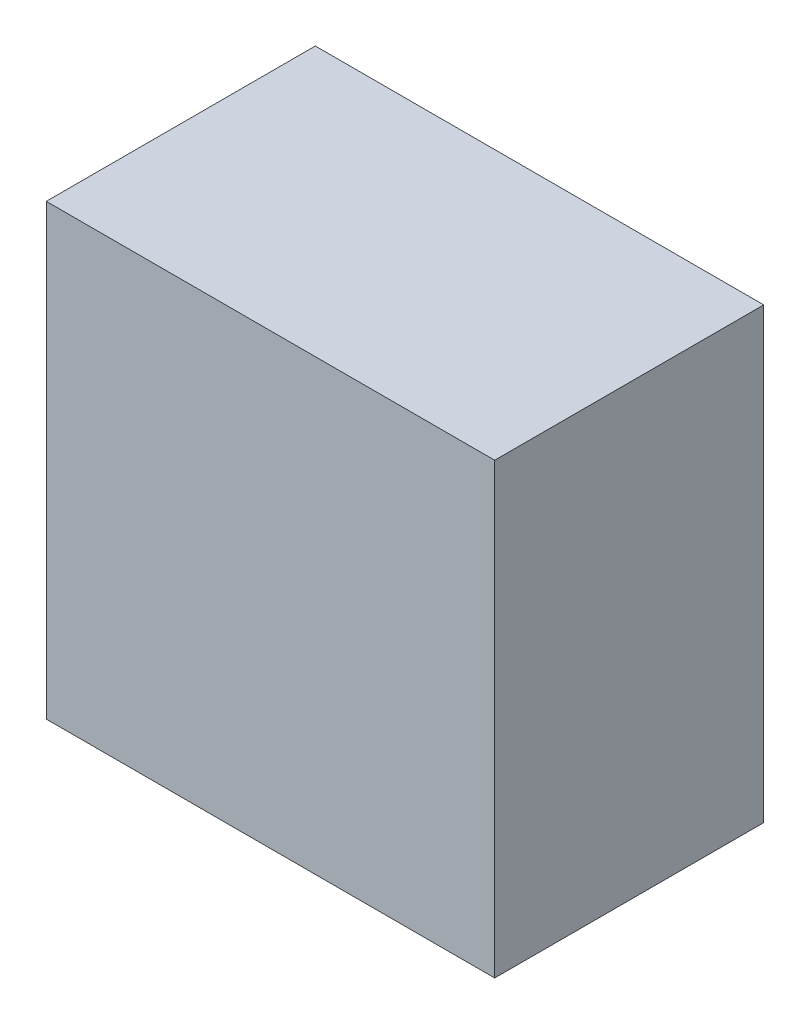
SolidWorks part; units mm, degrees
ref_plane "Front Plane" through (0, 0, 0) normal (0, 0, 1) x (1, 0, 0)
ref_plane "Top Plane" through (0, 0, 0) normal (0, 1, 0) x (1, 0, 0)
ref_plane "Right Plane" through (0, 0, 0) normal (1, 0, 0) x (0, 0, -1)
sketch "Sketch2" plane through (0, 0, 0) normal (0, 0, 1) x (1, 0, 0)
  line L1 (7.8014, -21.6312) -> (57.8014, -21.6312)
  line L2 (7.8014, -21.6312) -> (7.8014, 28.3688)
  line L3 (7.8014, 28.3688) -> (57.8014, 28.3688)
  line L4 (57.8014, -21.6312) -> (57.8014, 28.3688)
  dimension "D1" = 50
  dimension "D2" = 50
extrude "Boss-Extrude2" add sketch "Sketch2" against normal blind 30
sketch "Sketch3" plane through (0, 0, -30) normal (0, 0, -1) x (-1, 0, 0)
  line L0 (-7.8014, 28.3688) -> (-7.8014, -21.6312) construction
  line L1 (-10.3014, -19.1312) -> (-55.3014, -19.1312)
  line L2 (-10.3014, -19.1312) -> (-10.3014, 25.8688)
  line L3 (-10.3014, 25.8688) -> (-55.3014, 25.8688)
  line L4 (-55.3014, -19.1312) -> (-55.3014, 25.8688)
  line L5 (-57.8014, -21.6312) -> (-57.8014, 28.3688) construction
  line L6 (-7.8014, -21.6312) -> (-57.8014, -21.6312) construction
  line L7 (-57.8014, 28.3688) -> (-7.8014, 28.3688) construction
  dimension "D1" = 2.5
  dimension "D2" = 2.5
  dimension "D3" = 2.5
  dimension "D4" = 2.5
extrude "Cut-Extrude1" cut sketch "Sketch3" against normal blind 27
